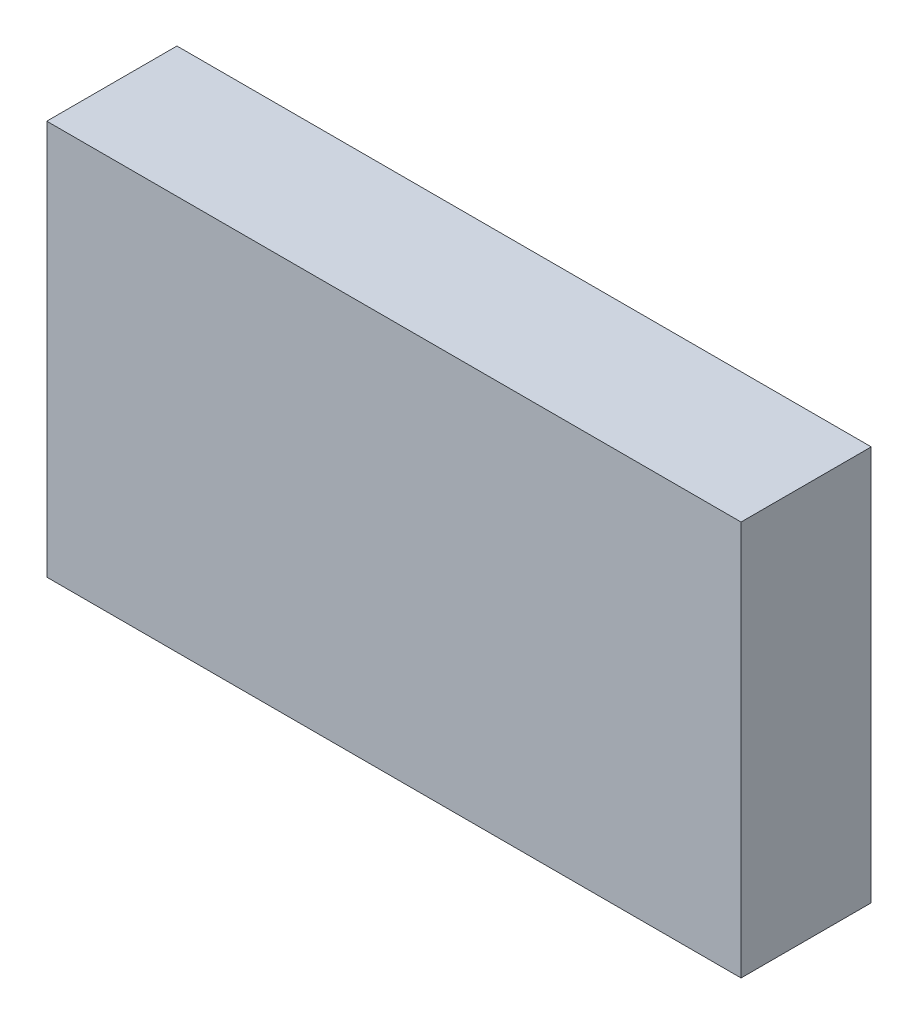
SolidWorks part; units mm, degrees
ref_plane "Front Plane" through (0, 0, 0) normal (0, 0, 1) x (1, 0, 0)
ref_plane "Top Plane" through (0, 0, 0) normal (0, 1, 0) x (1, 0, 0)
ref_plane "Right Plane" through (0, 0, 0) normal (1, 0, 0) x (0, 0, -1)
sketch "Sketch1" plane through (0, 0, 0) normal (0, 0, 1) x (1, 0, 0)
  line L1 (80, -45.5) -> (-80, -45.5)
  line L2 (80, -45.5) -> (80, 45.5)
  line L3 (80, 45.5) -> (-80, 45.5)
  line L4 (-80, -45.5) -> (-80, 45.5)
  line L5 (80, -45.5) -> (-80, 45.5) construction
  line L6 (80, 45.5) -> (-80, -45.5) construction
  point P0 (0, 0)
  dimension "D1" = 160
  dimension "D2" = 91
extrude "Boss-Extrude1" add sketch "Sketch1" along normal blind 30
